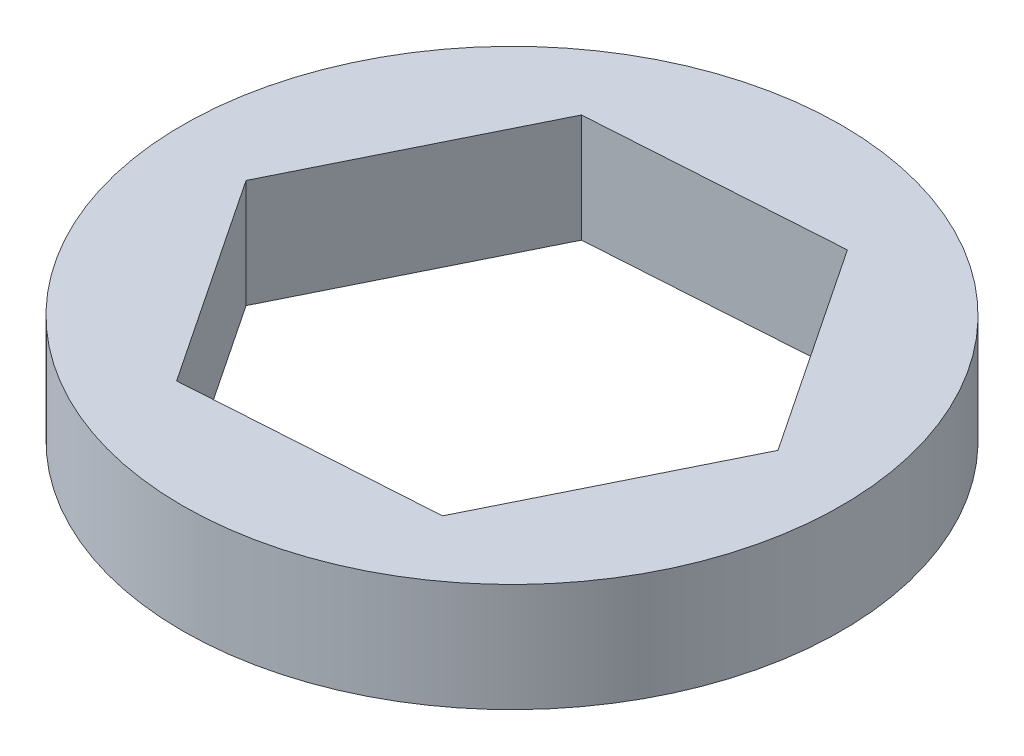
SolidWorks part; units mm, degrees
ref_plane "Front Plane" through (0, 0, 0) normal (0, 0, 1) x (1, 0, 0)
ref_plane "Top Plane" through (0, 0, 0) normal (0, 1, 0) x (1, 0, 0)
ref_plane "Right Plane" through (0, 0, 0) normal (1, 0, 0) x (0, 0, -1)
sketch "Sketch1" plane through (0, 0, 0) normal (0, 1, 0) x (1, 0, 0)
  line L1 (4.0673, -6.1009) -> (7.3171, 0.4719)
  line L2 (7.3171, 0.4719) -> (3.2499, 6.5728)
  line L3 (3.2499, 6.5728) -> (-4.0673, 6.1009)
  line L4 (-4.0673, 6.1009) -> (-7.3171, -0.4719)
  line L5 (-7.3171, -0.4719) -> (-3.2499, -6.5728)
  line L6 (-3.2499, -6.5728) -> (4.0673, -6.1009)
  circle A0 centre (0, 0) radius 9.652
  circle A1 centre (0, 0) radius 6.35 construction
  dimension "D1" = 12.7
  dimension "D2" = 19.304
extrude "Boss-Extrude1" add sketch "Sketch1" along normal blind 3.175
